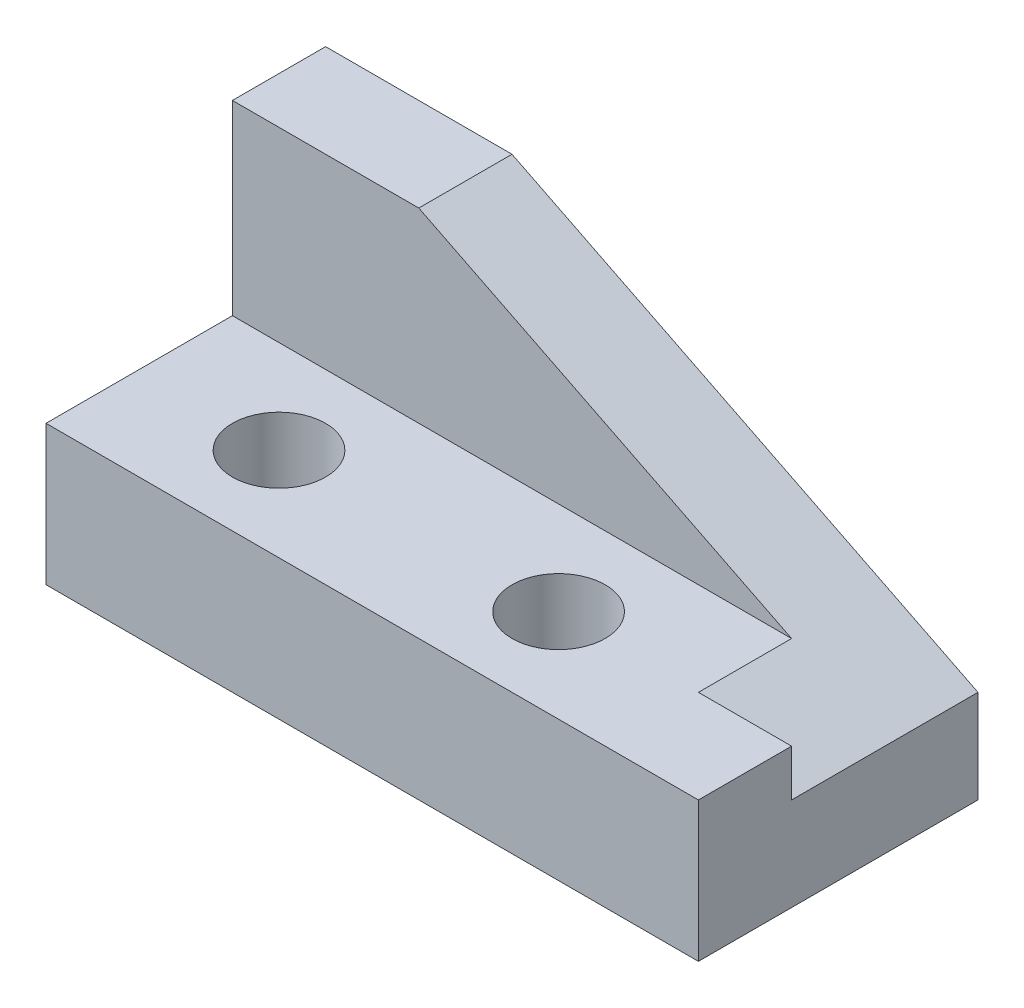
SolidWorks part; units mm, degrees
ref_plane "Front Plane" through (0, 0, 0) normal (0, 0, 1) x (1, 0, 0)
ref_plane "Top Plane" through (0, 0, 0) normal (0, 1, 0) x (1, 0, 0)
ref_plane "Right Plane" through (0, 0, 0) normal (1, 0, 0) x (0, 0, -1)
sketch "Sketch1" plane through (0, 0, 0) normal (0, 1, 0) x (1, 0, 0)
  line L1 (0, 0) -> (70, 0)
  line L2 (0, 0) -> (0, 30)
  line L3 (0, 30) -> (70, 30)
  line L4 (70, 0) -> (70, 30)
  dimension "D1" = 70
  dimension "D2" = 30
extrude "Boss-Extrude1" add sketch "Sketch1" along normal blind 35
sketch "Sketch2" plane through (0, 0, -30) normal (0, 0, -1) x (-1, 0, 0)
  line L0 (-70, 35) -> (-70, 10)
  line L1 (-70, 35) -> (-70, 0) construction
  line L2 (-70, 10) -> (-20, 35)
  line L3 (-70, 35) -> (0, 35) construction
  line L4 (-20, 35) -> (-70, 35)
  dimension "D1" = 50
  dimension "D2" = 25
extrude "Cut-Extrude1" cut sketch "Sketch2" against normal blind 20
sketch "Sketch3" plane through (0, 0, 0) normal (-1, 0, 0) x (0, 0, 1)
  line L1 (0, 35) -> (-20, 35)
  line L2 (0, 35) -> (0, 15)
  line L3 (0, 15) -> (-20, 15)
  line L4 (-20, 35) -> (-20, 15)
  dimension "D1" = 20
  dimension "D2" = 20
extrude "Cut-Extrude2" cut sketch "Sketch3" against normal through all
sketch "Sketch4" plane through (0, 15, 0) normal (0, 1, 0) x (1, 0, 0)
  line L0 (0, 0) -> (15, 0) construction
  line L1 (70, 0) -> (0, 0) construction
  line L2 (15, 0) -> (15, 10) construction
  circle A0 centre (15, 10) radius 5
  dimension "D3" = 10
  dimension "D1" = 15
  dimension "D2" = 10
extrude "Cut-Extrude3" cut sketch "Sketch4" against normal through all contours A0
sketch "Sketch5" plane through (0, 15, 0) normal (0, 1, 0) x (1, 0, 0)
  line L0 (0, 0) -> (45, 0) construction
  line L1 (70, 0) -> (0, 0) construction
  line L2 (45, 0) -> (45, 10) construction
  circle A0 centre (45, 10) radius 5
  dimension "D3" = 10
  dimension "D1" = 45
  dimension "D2" = 10
extrude "Cut-Extrude4" cut sketch "Sketch5" against normal through all
